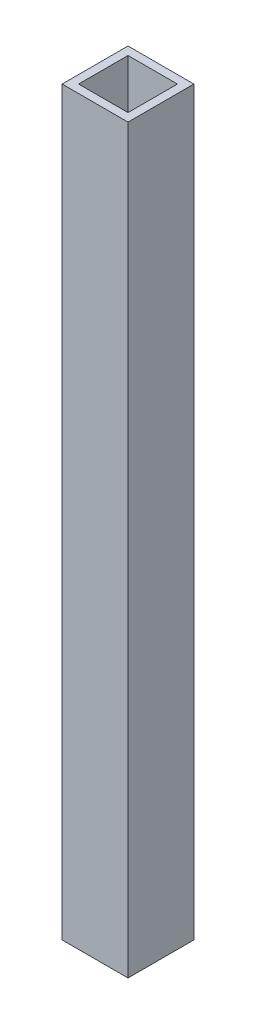
SolidWorks part; units mm, degrees
ref_plane "Piano frontale" through (0, 0, 0) normal (0, 0, 1) x (1, 0, 0)
ref_plane "Piano superiore" through (0, 0, 0) normal (0, 1, 0) x (1, 0, 0)
ref_plane "Piano destro" through (0, 0, 0) normal (1, 0, 0) x (0, 0, -1)
sketch "Schizzo1" plane through (0, 0, 0) normal (0, 1, 0) x (1, 0, 0)
  line L0 (15, 15) -> (-15, 15)
  line L1 (20, -20) -> (-20, -20)
  line L2 (20, -20) -> (20, 20)
  line L3 (20, 20) -> (-20, 20)
  line L4 (-20, -20) -> (-20, 20)
  line L5 (20, -20) -> (-20, 20) construction
  line L6 (20, 20) -> (-20, -20) construction
  line L7 (-15, -15) -> (-15, 15)
  line L8 (15, -15) -> (-15, -15)
  line L9 (15, -15) -> (15, 15)
  point P0 (0, 0)
  dimension "D1" = 40
  dimension "D2" = 40
  dimension "D3" = 5
extrude "Estrusione-Estrusione1" add sketch "Schizzo1" along normal mid plane 450
